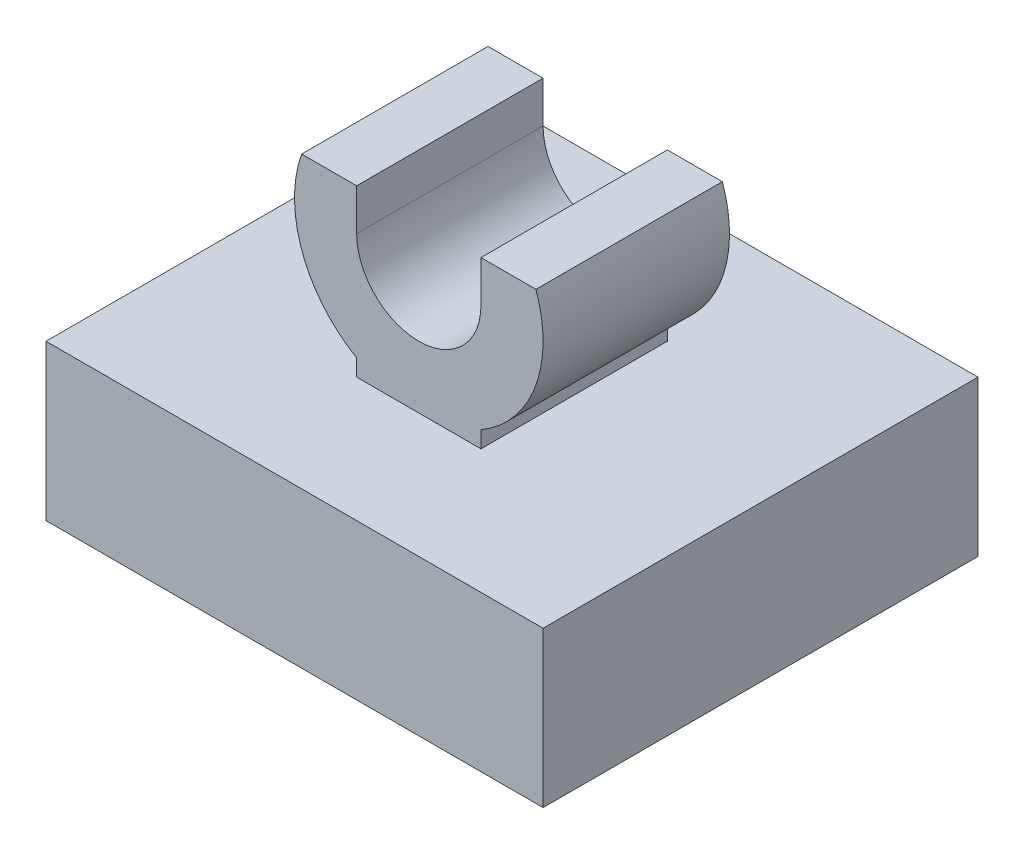
SolidWorks part; units mm, degrees
material "ABS"
ref_plane "Front Plane" through (0, 0, 0) normal (0, 0, 1) x (1, 0, 0)
ref_plane "Top Plane" through (0, 0, 0) normal (0, 1, 0) x (1, 0, 0)
ref_plane "Right Plane" through (0, 0, 0) normal (1, 0, 0) x (0, 0, -1)
sketch "Sketch1" plane through (0, 0, 0) normal (0, 0, 1) x (1, 0, 0)
  line L0 (-5.08, 0) -> (5.08, 0)
  line L1 (5.08, 0) -> (5.08, -3.175)
  line L2 (5.08, -3.175) -> (-5.08, -3.175)
  line L3 (-5.08, -3.175) -> (-5.08, 0)
  point P3 (0, -3.175)
  dimension "D1" = 10.16
  dimension "D2" = 3.175
extrude "Boss-Extrude1" add sketch "Sketch1" along normal mid plane 8.89
sketch "Sketch2" plane through (0, 0, 0) normal (0, 0, 1) x (1, 0, 0)
  line L0 (-1.27, 2.54) -> (-1.27, 3.3867)
  line L1 (1.27, 2.54) -> (1.27, 3.3867)
  line L2 (-2.3947, 3.3867) -> (-1.27, 3.3867)
  line L3 (1.27, 3.3867) -> (2.3947, 3.3867)
  line L4 (-1.27, 0.3403) -> (-1.27, 0)
  line L5 (5.08, 0) -> (-5.08, 0) construction
  line L6 (1.27, 0.3403) -> (1.27, 0)
  line L7 (-1.27, 0) -> (1.27, 0)
  arc A0 (-2.3947, 3.3867) -> (-1.27, 0.3403) centre (0, 2.54) ccw
  arc A1 (-1.27, 2.54) -> (1.27, 2.54) centre (0, 2.54) ccw
  arc A2 (1.27, 0.3403) -> (2.3947, 3.3867) centre (0, 2.54) ccw
  dimension "D1" = 5.08
  dimension "D2" = 2.54
extrude "Boss-Extrude2" add sketch "Sketch2" along normal mid plane 3.81
sketch "Sketch3" plane through (0, -3.175, 0) normal (0, -1, 0) x (1, 0, 0)
  line L0 (-2.54, 2.54) -> (-2.54, -2.54)
  line L1 (-2.54, -2.54) -> (2.54, -2.54)
  line L2 (2.54, -2.54) -> (2.54, 2.54)
  line L3 (2.54, 2.54) -> (-2.54, 2.54)
  line L4 (-5.08, -4.445) -> (5.08, -4.445)
  line L5 (5.08, -4.445) -> (5.08, 4.445)
  line L6 (5.08, 4.445) -> (-5.08, 4.445)
  line L7 (-5.08, 4.445) -> (-5.08, -4.445)
  line L8 (-5.08, -4.445) -> (5.08, -4.445)
  line L9 (5.08, -4.445) -> (5.08, 4.445)
  line L10 (5.08, 4.445) -> (-5.08, 4.445)
  line L11 (-5.08, 4.445) -> (-5.08, -4.445)
  dimension "D1" = 0
extrude "Cut-Extrude1" cut sketch "Sketch3" against normal blind 1.905 flip side to cut
